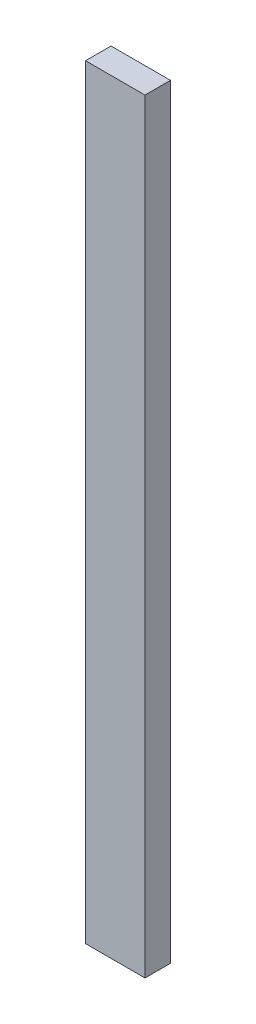
SolidWorks part; units mm, degrees
material "Oak"
ref_plane "Front Plane" through (0, 0, 0) normal (0, 0, 1) x (1, 0, 0)
ref_plane "Top Plane" through (0, 0, 0) normal (0, 1, 0) x (1, 0, 0)
ref_plane "Right Plane" through (0, 0, 0) normal (1, 0, 0) x (0, 0, -1)
sketch "Sketch1" plane through (0, 0, 0) normal (0, 1, 0) x (1, 0, 0)
  line L1 (-44.45, -19.05) -> (44.45, -19.05)
  line L2 (-44.45, -19.05) -> (-44.45, 19.05)
  line L3 (-44.45, 19.05) -> (44.45, 19.05)
  line L4 (44.45, -19.05) -> (44.45, 19.05)
  line L5 (-44.45, -19.05) -> (44.45, 19.05) construction
  line L6 (-44.45, 19.05) -> (44.45, -19.05) construction
  point P0 (0, 0)
  dimension "D1" = 38.1
  dimension "D2" = 88.9
extrude "Boss-Extrude1" add sketch "Sketch1" along normal blind 1143 contours L3 L4 L1 L2
